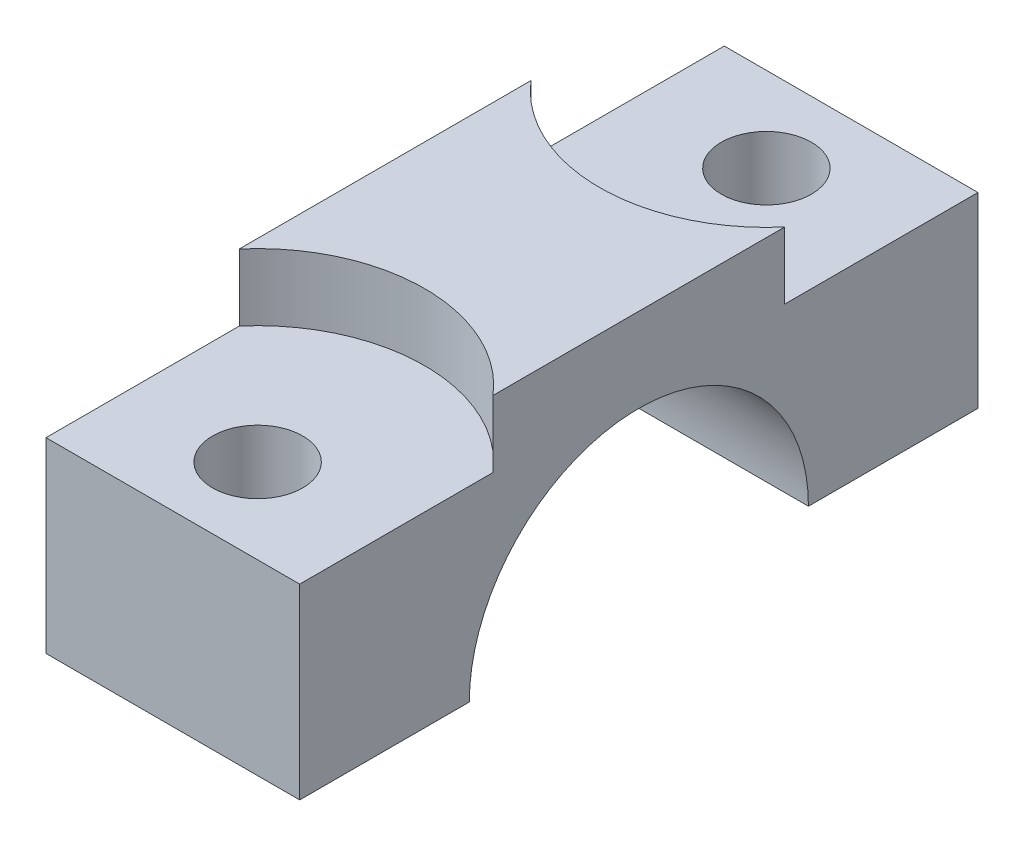
SolidWorks part; units mm, degrees
ref_plane "Front Plane" through (0, 0, 0) normal (0, 0, 1) x (1, 0, 0)
ref_plane "Top Plane" through (0, 0, 0) normal (0, 1, 0) x (1, 0, 0)
ref_plane "Right Plane" through (0, 0, 0) normal (1, 0, 0) x (0, 0, -1)
sketch "Sketch1" plane through (0, 0, 0) normal (1, 0, 0) x (0, 0, -1)
  line L1 (-25.4, 0) -> (25.4, 0)
  line L2 (-25.4, 0) -> (-25.4, 19)
  line L3 (-25.4, 19) -> (25.4, 19)
  line L4 (25.4, 0) -> (25.4, 19)
  circle A0 centre (0, 0) radius 12.7
  point P7 (0, 0)
  dimension "D3" = 25.4
  dimension "D1" = 19
  dimension "D2" = 50.8
extrude "Boss-Extrude1" add sketch "Sketch1" along normal mid plane 19 contours A0 L1 L4 L3 L2
sketch "Sketch2" plane through (0, 0, 0) normal (0, -1, 0) x (1, 0, 0)
  line L0 (0, 25.4) -> (0, 12.7) construction
  line L1 (9.5, 25.4) -> (-9.5, 25.4) construction
  line L2 (9.5, 12.7) -> (-9.5, 12.7) construction
  line L3 (0, -12.7) -> (0, -25.4) construction
  line L4 (9.5, -12.7) -> (-9.5, -12.7) construction
  line L5 (9.5, -25.4) -> (-9.5, -25.4) construction
  point P14 (0, -19.05)
  point P15 (0, 19.05)
sketch "Sketch7" plane through (0, 19, 0) normal (0, 1, 0) x (1, 0, 0)
  line L0 (0, 25.4) -> (0, 12.7) construction
  line L1 (0, -25.4) -> (0, -12.7) construction
  point P8 (0, 19.05)
  point P9 (0, -19.05)
hole_wizard "CBORE for M12 Hex Head Cap Screw1" positions "3DSketch5" profile "Sketch8" counterbore size "M12" standard "ISO" end condition through all
sketch3d "3DSketch5"
  point P0 (0, 19, -19.05)
  point P3 (0, 19, 19.05)
sketch "Sketch8" plane through (0, 19, -19.05) normal (1, 0, 0) x (0, 0, 1)
  line L0 (0, 0) -> (0, 19)
  line L1 (0, 19) -> (3.375, 19)
  line L3 (3.375, 19) -> (3.375, 5)
  line L4 (3.375, 5) -> (12.5, 5)
  line L5 (12.5, 5) -> (12.5, 0)
  line L7 (12.5, 0) -> (0, 0)
  line L11 (0, -6.35) -> (0, 107.95) construction
  dimension "Thru Hole Dia." = 6.75
  dimension "Thru Hole Depth" = 19
  dimension "C'Bore Dia." = 25
  dimension "C'Bore Depth" = 5
